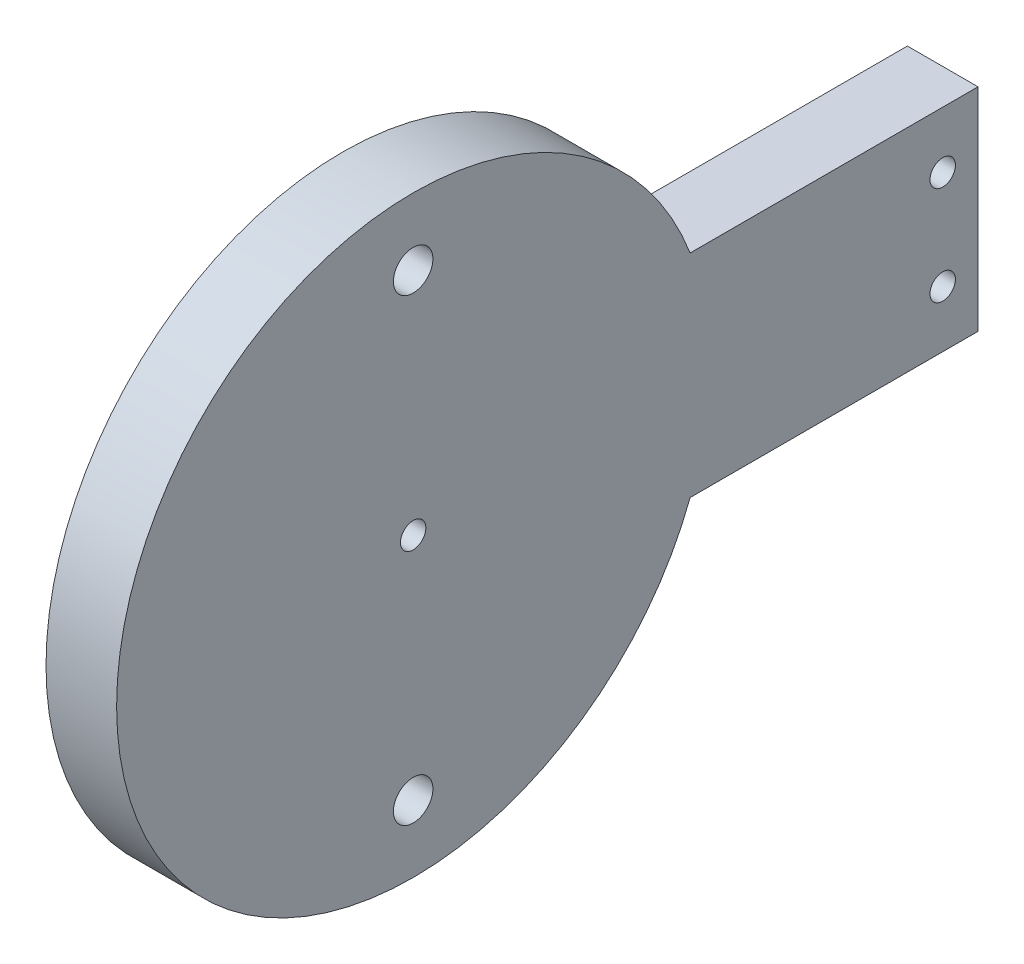
SolidWorks part; units mm, degrees
ref_plane "정면" through (0, 0, 0) normal (0, 0, 1) x (1, 0, 0)
ref_plane "윗면" through (0, 0, 0) normal (0, 1, 0) x (1, 0, 0)
ref_plane "우측면" through (0, 0, 0) normal (1, 0, 0) x (0, 0, -1)
ref_plane "평면1" through (-9, 0, 0) normal (-1, 0, 0) x (0, -1, 0)
sketch "스케치1" plane through (-9, 0, 0) normal (-1, 0, 0) x (0, -1, 0)
  line L0 (-21, -18.1229) -> (-21, 2.2621)
  line L1 (-6, -18.1229) -> (-6, 2.2621)
  line L3 (-13.5, 21.8771) -> (7.5, 21.8771) construction
  line L4 (7.5, 21.8771) -> (-34.5, 21.8771) construction
  line L5 (-13.5, 21.8771) -> (-13.5, -66.3671) construction
  line L8 (-21, -18.1229) -> (-6, -18.1229)
  circle A1 centre (-13.5, 21.8771) radius 21 construction
  circle A2 centre (-13.5, 21.8771) radius 30 construction
  arc A3 (-6, 2.2621) -> (-21, 2.2621) centre (-13.5, 21.8771) ccw
  point P12 (7.5, 0.4528)
  point P17 (-34.5, 0.4528)
  dimension "D2" = 40
extrude "보스-돌출1" add sketch "스케치1" against normal blind 5
ref_plane "평면2" through (0, 13.5, 0) normal (0, 1, 0) x (1, 0, 0)
sketch "스케치6" plane through (-4, 0, 0) normal (1, 0, 0) x (0, 0, -1)
  line L0 (-2.2621, 21) -> (18.1229, 21) construction
  line L1 (18.1229, 6) -> (13.1229, 6)
  line L2 (18.1229, 6) -> (18.1229, 21)
  line L3 (18.1229, 21) -> (13.1229, 21)
  line L4 (13.1229, 6) -> (13.1229, 21)
  dimension "D1" = 5
sketch "스케치8" plane through (-9, 0, 0) normal (-1, 0, 0) x (0, 0, 1)
  line L0 (-18.1229, 21) -> (-13.1229, 21) construction
  line L1 (-18.1229, 6) -> (-13.1229, 6) construction
  line L2 (-18.1229, 21) -> (-18.1229, 6) construction
  line L3 (21.8771, 13.5) -> (21.8771, 62.4132) construction
  line L4 (21.8771, 62.4132) -> (21.8771, -53.5206) construction
  circle A0 centre (21.8771, 13.5) radius 0.9
  circle A1 centre (-15.6229, 17) radius 0.9
  circle A2 centre (-15.6229, 10) radius 0.9
  circle A3 centre (21.8771, 29.75) radius 1.4
  circle A4 centre (21.8771, -2.75) radius 1.4
  dimension "D1" = 1.8
  dimension "D2" = 1.8
  dimension "D3" = 1.8
  dimension "D8" = 2.8
  dimension "D9" = 2.8
  dimension "D10" = 32.5
  dimension "D4" = 4
  dimension "D5" = 4
  dimension "D6" = 2.5
  dimension "D7" = 2.5
  dimension "D11" = 16.25
extrude "컷-돌출3" cut sketch "스케치8" against normal blind 10
